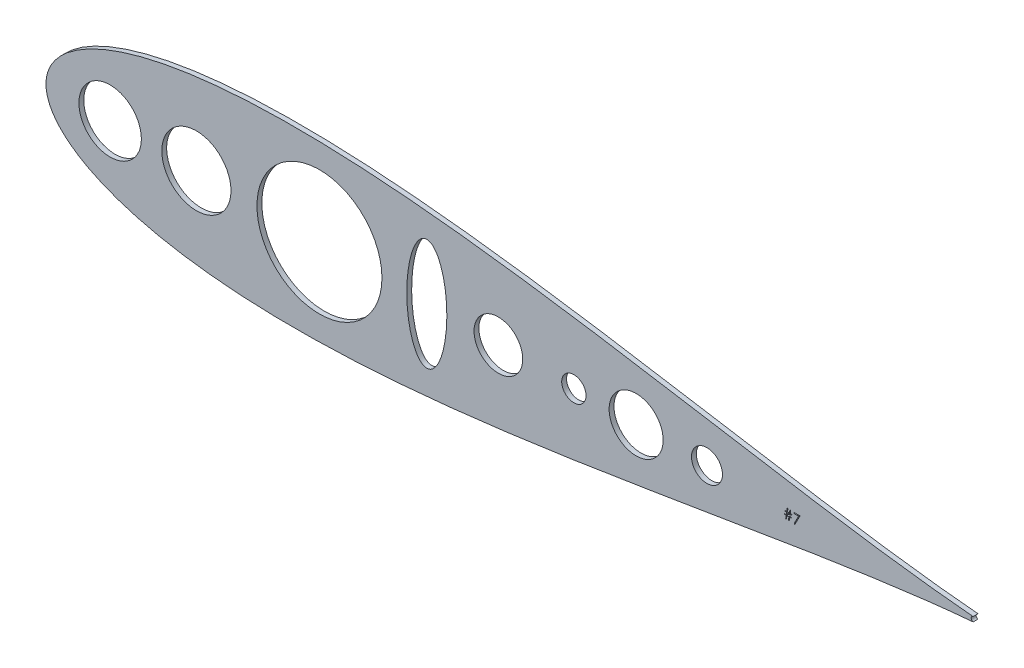
SolidWorks part; units mm, degrees
ref_plane "Front Plane" through (0, 0, 0) normal (0, 0, 1) x (1, 0, 0)
ref_plane "Top Plane" through (0, 0, 0) normal (0, 1, 0) x (1, 0, 0)
ref_plane "Right Plane" through (0, 0, 0) normal (1, 0, 0) x (0, 0, -1)
sketch "Sketch2" plane through (0, 0, 0) normal (0, 0, 1) x (1, 0, 0)
  line L0 (672.2866, 533.3885) -> (672.2866, 533.0629)
  line L1 (672.2866, 533.0629) -> (671.3157, 533.0629)
  line L2 (671.3157, 533.0629) -> (671.0522, 531.3044)
  line L3 (671.0522, 531.3044) -> (670.6584, 531.3044)
  line L4 (670.6584, 531.3044) -> (670.9219, 533.0629)
  line L5 (670.9219, 533.0629) -> (669.8829, 533.0629)
  line L6 (669.8829, 533.0629) -> (669.6194, 531.3044)
  line L7 (669.6194, 531.3044) -> (669.2255, 531.3044)
  line L8 (669.2255, 531.3044) -> (669.4891, 533.0629)
  line L9 (669.4891, 533.0629) -> (668.6394, 533.0629)
  line L10 (668.6394, 533.0629) -> (668.6394, 533.3885)
  line L11 (668.6394, 533.3885) -> (669.5379, 533.3885)
  line L12 (669.5379, 533.3885) -> (669.714, 534.5608)
  line L13 (669.714, 534.5608) -> (668.7696, 534.5608)
  line L14 (668.7696, 534.5608) -> (668.7696, 534.8865)
  line L15 (668.7696, 534.8865) -> (669.7628, 534.8865)
  line L16 (669.7628, 534.8865) -> (670.0071, 536.5147)
  line L17 (670.0071, 536.5147) -> (670.3999, 536.5147)
  line L18 (670.3999, 536.5147) -> (670.1556, 534.8865)
  line L19 (670.1556, 534.8865) -> (671.1957, 534.8865)
  line L20 (671.1957, 534.8865) -> (671.4399, 536.5147)
  line L21 (671.4399, 536.5147) -> (671.8327, 536.5147)
  line L22 (671.8327, 536.5147) -> (671.5885, 534.8865)
  line L23 (671.5885, 534.8865) -> (672.4168, 534.8865)
  line L24 (672.4168, 534.8865) -> (672.4168, 534.5608)
  line L25 (672.4168, 534.5608) -> (671.5396, 534.5608)
  line L26 (671.5396, 534.5608) -> (671.3646, 533.3885)
  line L27 (671.3646, 533.3885) -> (672.2866, 533.3885)
  line L28 (671.1468, 534.5608) -> (670.1068, 534.5608)
  line L29 (670.1068, 534.5608) -> (669.9318, 533.3885)
  line L30 (669.9318, 533.3885) -> (670.9708, 533.3885)
  line L31 (670.9708, 533.3885) -> (671.1468, 534.5608)
  line L32 (673.5891, 536.3844) -> (676.7153, 536.3844)
  line L33 (676.7153, 536.3844) -> (674.045, 531.1741)
  line L34 (674.045, 531.1741) -> (673.6512, 531.3909)
  line L35 (673.6512, 531.3909) -> (675.9439, 535.8634)
  line L36 (675.9439, 535.8634) -> (673.5891, 535.8634)
  line L37 (673.5891, 535.8634) -> (673.5891, 536.3844)
  circle A0 centre (316.9415, 534.8483) radius 16.2849
  circle A1 centre (628.1831, 534.8483) radius 8.0865
  circle A2 centre (591.2438, 534.8483) radius 14.0957
  circle A3 centre (558.7673, 534.8483) radius 6.35
  circle A4 centre (519.3973, 534.8483) radius 12.7
  circle A5 centre (426.1032, 534.8483) radius 32.5896
  circle A6 centre (361.9173, 534.8483) radius 18.034
  arc A7 (766.9747, 536.0676) -> (766.9717, 533.6287) centre (767.2222, 534.8479) ccw
  ellipse E0 centre (482.0882, 534.8483) end of major axis (482.0882, 505.747) minor radius 10.4447
  spline S0 degree 3 poles (766.9747, 536.0676) (766.6971, 536.0909) (763.8731, 536.3296) (758.2015, 536.8538) (749.6175, 537.7468) (740.1002, 538.8425) (729.6855, 540.1476) (718.4217, 541.6634) (706.3578, 543.3865) (693.5458, 545.308) (680.0403, 547.4141) (665.8978, 549.6862) (651.1768, 552.1008) (635.9373, 554.6299) (620.241, 557.2418) (604.1511, 559.9008) (587.7317, 562.5686) (571.0485, 565.2042) (554.1682, 567.7646) (537.1589, 570.2057) (520.0896, 572.4831) (503.0308, 574.5523) (486.0541, 576.3696) (469.2323, 577.8932) (452.6394, 579.0834) (436.3507, 579.9034) (420.4428, 580.3201) (404.9933, 580.3046) (390.081, 579.8324) (375.7861, 578.885) (362.1901, 577.4487) (349.3761, 575.517) (337.4295, 573.0892) (326.4387, 570.1734) (316.4967, 566.7868) (307.7025, 562.9594) (300.1631, 558.7421) (293.991, 554.2203) (289.2902, 549.5417) (286.1076, 544.9538) (284.3329, 540.8146) (283.6163, 537.4942) (283.4531, 534.8483) (283.6163, 532.2024) (284.3329, 528.882) (286.1076, 524.7428) (289.2902, 520.1548) (293.991, 515.4763) (300.1631, 510.9545) (307.7025, 506.7371) (316.4967, 502.9098) (326.4387, 499.5231) (337.4295, 496.6074) (349.3761, 494.1796) (362.1901, 492.2478) (375.7861, 490.8115) (390.081, 489.8641) (404.9933, 489.392) (420.4428, 489.3765) (436.3507, 489.7932) (452.6394, 490.6132) (469.2323, 491.8033) (486.0541, 493.327) (503.0308, 495.1443) (520.0896, 497.2135) (537.1589, 499.4908) (554.1682, 501.932) (571.0485, 504.4924) (587.7317, 507.1279) (604.1511, 509.7957) (620.241, 512.4548) (635.9373, 515.0666) (651.1768, 517.5958) (665.8978, 520.0103) (680.0403, 522.2824) (693.5458, 524.3886) (706.3578, 526.3101) (718.4217, 528.0332) (729.6855, 529.5489) (740.1002, 530.854) (749.6175, 531.9498) (758.2015, 532.8428) (763.8721, 533.3669) (766.6951, 533.6055) (766.9717, 533.6287) knots 0.020477 0.020477 0.020477 0.020477 0.021271 0.028553 0.036781 0.04592 0.055932 0.066773 0.078397 0.090755 0.103793 0.117456 0.131686 0.146422 0.1616 0.177156 0.193024 0.209135 0.225421 0.241812 0.258238 0.274629 0.290914 0.307025 0.322893 0.338448 0.353626 0.368361 0.38259 0.396253 0.40929 0.421647 0.43327 0.444109 0.454119 0.463255 0.471479 0.478755 0.485052 0.490344 0.49461 0.497833 0.5 0.502167 0.50539 0.509656 0.514948 0.521245 0.528521 0.536745 0.545881 0.555891 0.56673 0.578353 0.59071 0.603747 0.61741 0.631639 0.646374 0.661552 0.677107 0.692975 0.709086 0.725371 0.741762 0.758188 0.774579 0.790865 0.806976 0.822844 0.8384 0.853578 0.868314 0.882544 0.896207 0.909245 0.921603 0.933227 0.944068 0.95408 0.963219 0.971447 0.978729 0.97952 0.97952 0.97952 0.97952
extrude "Boss-Extrude1" add sketch "Sketch2" along normal blind 2.54 contours A7 S0 L36 L37 L32 L33 L34 L35 L26 L27 L0 L1 L2 L3 L4 L5 L6 L7 L8 L9 L10 L11 L12 L13 L14 L15 L16 L17 L18 L19 L20 L21 L22 L23 L24 L25 A0 A1 A2 A3 A4 A5
